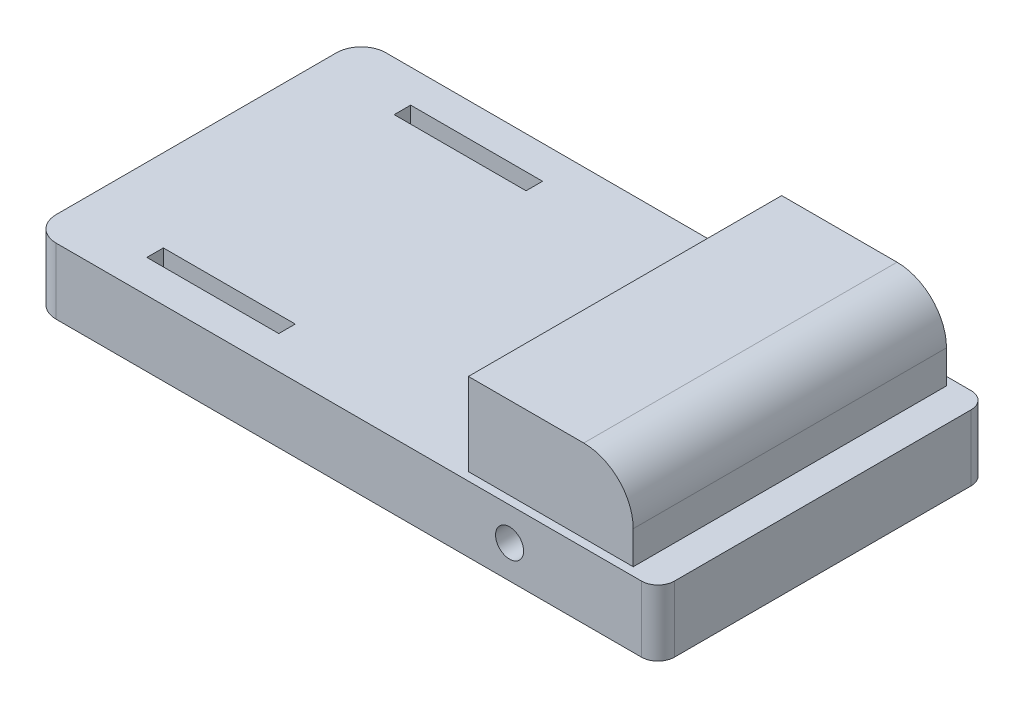
SolidWorks part; units mm, degrees
ref_plane "Front Plane" through (0, 0, 0) normal (0, 0, 1) x (1, 0, 0)
ref_plane "Top Plane" through (0, 0, 0) normal (0, 1, 0) x (1, 0, 0)
ref_plane "Right Plane" through (0, 0, 0) normal (1, 0, 0) x (0, 0, -1)
sketch "Sketch1" plane through (0, 0, 0) normal (0, 1, 0) x (1, 0, 0)
  line L0 (-482.6, 254) -> (482.6, -254) construction
  line L1 (-482.6, 254) -> (482.6, 254)
  line L2 (-482.6, 254) -> (-482.6, -254)
  line L3 (-482.6, -254) -> (482.6, -254)
  line L4 (482.6, 254) -> (482.6, -254)
  dimension "D1" = 965.2
  dimension "D2" = 508
extrude "Boss-Extrude1" add sketch "Sketch1" along normal blind 101.6
sketch "Sketch2" plane through (0, 0, 254) normal (0, 0, 1) x (1, 0, 0)
  line L0 (-482.6, 50.8) -> (482.6, 50.8) construction
  line L1 (-482.6, 101.6) -> (-482.6, 0) construction
  line L2 (482.6, 101.6) -> (482.6, 0) construction
  circle A1 centre (254, 50.8) radius 21.59
  point P6 (-254, 50.8)
  point P7 (254, 50.8)
  dimension "D4" = 43.18
  dimension "D1" = 228.6
  dimension "D2" = 228.6
extrude "Cut-Extrude1" cut sketch "Sketch2" against normal through all
fillet "Fillet1" radius 38.1 2 edges at (-482.6, 50.8, -254) (-482.6, 50.8, 254)
fillet "Fillet2" radius 25.4 2 edges at (482.6, 50.8, 254) (482.6, 50.8, -254)
sketch "Sketch4" plane through (0, 101.6, 0) normal (0, 1, 0) x (1, 0, 0)
  line L0 (-254, 254) -> (-254, -254) construction
  line L1 (457.2, 254) -> (-444.5, 254) construction
  line L2 (-444.5, -254) -> (457.2, -254) construction
  line L3 (-482.6, 215.9) -> (-482.6, -215.9) construction
  line L4 (-254, 0) -> (-355.6, 0) construction
  line L5 (-355.6, -177.8) -> (-152.4, -177.8)
  line L6 (-355.6, -177.8) -> (-355.6, -203.2)
  line L7 (-355.6, -203.2) -> (-152.4, -203.2)
  line L8 (-152.4, -177.8) -> (-152.4, -203.2)
  line L9 (-355.6, 177.8) -> (-355.6, 203.2)
  line L10 (-355.6, 203.2) -> (-152.4, 203.2)
  line L11 (-152.4, 177.8) -> (-152.4, 203.2)
  line L12 (-355.6, 177.8) -> (-152.4, 177.8)
  point P12 (-254, -177.8)
  dimension "D1" = 228.6
  dimension "D2" = 25.4
  dimension "D3" = 50.8
  dimension "D4" = 203.2
extrude "Cut-Extrude2" cut sketch "Sketch4" against normal up to next
sketch "Sketch6" plane through (0, 101.6, 0) normal (0, 1, 0) x (1, 0, 0)
  line L0 (482.6, 0) -> (177.8828, 0) construction
  line L1 (482.6, -228.6) -> (482.6, 228.6) construction
  line L2 (457.2, 254) -> (-444.5, 254) construction
  line L3 (177.8828, 241.3) -> (431.8, 241.3)
  line L4 (177.8828, 241.3) -> (177.8828, -241.3)
  line L5 (177.8828, -241.3) -> (431.8, -241.3)
  line L6 (431.8, 241.3) -> (431.8, -241.3)
  line L7 (-444.5, -254) -> (457.2, -254) construction
  dimension "D1" = 12.7
  dimension "D2" = 12.7
  dimension "D3" = 50.8
extrude "Boss-Extrude3" add sketch "Sketch6" along normal blind 127
fillet "Fillet4" radius 76.2 1 edges at (431.8, 228.6, 0)
sketch "Sketch7" plane through (177.8828, 0, 0) normal (-1, 0, 0) x (0, 0, 1)
  line L0 (-241.3, 228.6) -> (-241.3, 101.6) construction
  line L1 (-228.6, 215.9) -> (228.6, 215.9)
  line L2 (-228.6, 215.9) -> (-228.6, 101.6)
  line L3 (-228.6, 101.6) -> (228.6, 101.6)
  line L4 (228.6, 215.9) -> (228.6, 101.6)
  line L5 (-241.3, 228.6) -> (241.3, 228.6) construction
  line L6 (241.3, 228.6) -> (241.3, 101.6) construction
  line L7 (-241.3, 101.6) -> (241.3, 101.6) construction
  dimension "D1" = 12.7
  dimension "D2" = 12.7
  dimension "D3" = 12.7
extrude "Cut-Extrude4" cut sketch "Sketch7" against normal blind 179
